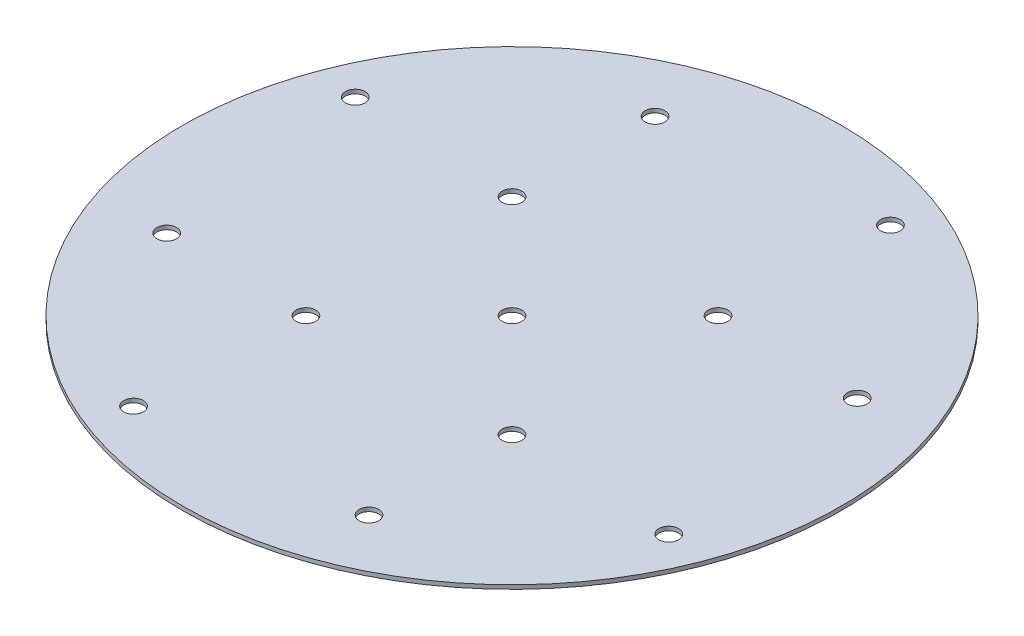
SolidWorks part; units mm, degrees
material "6061-T6 (SS)"
ref_plane "Front Plane" through (0, 0, 0) normal (0, 0, 1) x (1, 0, 0)
ref_plane "Top Plane" through (0, 0, 0) normal (0, 1, 0) x (1, 0, 0)
ref_plane "Right Plane" through (0, 0, 0) normal (1, 0, 0) x (0, 0, -1)
sketch "Sketch2" plane through (0, 0, 0) normal (1, 0, 0) x (0, 0, -1)
  line L0 (0, 0) -> (-82.55, 0)
  line L1 (-82.55, 0) -> (-82.55, 1)
  line L2 (-82.55, 1) -> (0, 1)
  line L5 (0, 1) -> (0, 0)
  dimension "D1" = 82.55
  dimension "D2" = 1
ref_axis "Axis1" through (0, -0.05, 0) along (0, 1, 0)
revolve "Revolve1" add sketch "Sketch2" angle 360 about axis through (0, -0.05, 0) along (0, 1, 0)
hole_wizard "#10 (0.1935) Diameter Hole1" positions "Sketch6" profile "Sketch7" hole size "#10" standard "ANSI Inch" end condition through all
sketch "Sketch6" plane through (0, 1, 0) normal (0, 1, 0) x (1, 0, 0)
  line L0 (0, 0) -> (-53.438, 129.0108) construction
  line L2 (0, 0) -> (0, 109.0908) construction
  line L3 (0, 0) -> (-76.2663, 31.5905) construction
  line L4 (0, 0) -> (-47.7784, 47.7784) construction
  circle A0 centre (0, 0) radius 82.55 construction
  point P0 (-25.3336, 61.1608)
  point P11 (264.7437, 73.7878)
  point P20 (-67.0275, 27.7637)
  point P22 (-25.8094, 25.8094)
  dimension "D1" = 22.5
  dimension "D2" = 66.2
  dimension "D3" = 72.55
  dimension "D4" = 45
  dimension "D6" = 22.5
  dimension "D5" = 36.5
sketch "Sketch7" plane through (-25.3336, 1, -61.1608) normal (1, 0, 0) x (0, 0, 1)
  line L0 (0, 0) -> (0, 1)
  line L1 (0, 1) -> (2.4574, 1)
  line L2 (2.4574, 1) -> (2.4574, 0)
  line L5 (2.4574, 0) -> (0, 0)
  line L11 (0, -6.35) -> (0, 107.95) construction
  dimension "Thru Hole Dia." = 4.9149
  dimension "Thru Hole Depth" = 1
pattern_circular "CirPattern3" count 4 over 360 about axis through (0, 0, 0) along (0, 1, 0) of "#10 (0.1935) Diameter Hole1"
hole_wizard "#10 (0.1935) Diameter Hole2" positions "Sketch8" profile "Sketch9" hole size "#10" standard "ANSI Inch" end condition through all
sketch "Sketch8" plane through (0, 1, 0) normal (0, 1, 0) x (1, 0, 0)
  line L0 (0, 0) -> (106.3094, -1.7118) construction
  point P7 (0, 0)
sketch "Sketch9" plane through (0, 1, 0) normal (1, 0, 0) x (0, 0, 1)
  line L0 (0, 0) -> (0, 1)
  line L1 (0, 1) -> (2.4574, 1)
  line L2 (2.4574, 1) -> (2.4574, 0)
  line L5 (2.4574, 0) -> (0, 0)
  line L11 (0, -6.35) -> (0, 107.95) construction
  dimension "Thru Hole Dia." = 4.9149
  dimension "Thru Hole Depth" = 1
equation "\"TubeDiameter\" = 6.500in"
equation "\"D1@Sketch2\"=\"TubeDiameter\"/2"
equation "\"D2@Sketch6\"=66.2"
equation "\"D3@Sketch6\"=\"TubeDiameter\"/2-10mm"
